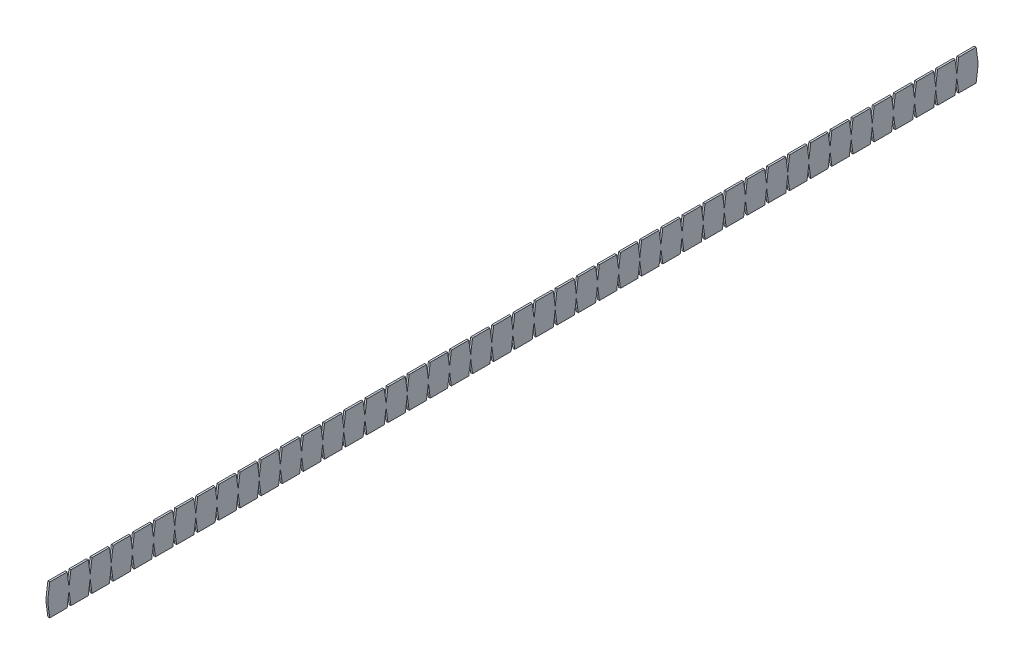
SolidWorks part; units mm, degrees
ref_plane "Front Plane" through (0, 0, 0) normal (0, 0, 1) x (1, 0, 0)
ref_plane "Top Plane" through (0, 0, 0) normal (0, 1, 0) x (1, 0, 0)
ref_plane "Right Plane" through (0, 0, 0) normal (1, 0, 0) x (0, 0, -1)
sketch "Sketch2" plane through (0, 0, 0) normal (1, 0, 0) x (0, 0, -1)
  line L9 (-34.544, 0) -> (-31.496, 22.86)
  line L10 (-31.496, 22.86) -> (-3.048, 22.86)
  line L94 (-3.048, 22.86) -> (0, 0)
  line L187 (-34.544, 0) -> (-34.544, -5.08)
  line L255 (-3.048, -27.94) -> (0, -5.08)
  line L256 (-31.496, -27.94) -> (-3.048, -27.94)
  line L257 (-34.544, -5.08) -> (-31.496, -27.94)
  line L262 (0, 0) -> (0, -5.08)
  dimension "D1" = 28.448
  dimension "D2" = 34.544
  dimension "D3" = 5.08
  dimension "D4" = 50.8
extrude "Boss-Extrude1" add sketch "Sketch2" along normal blind 3.048
pattern_linear "LPattern1" count 44 spacing 34.544 along (0, 0, -1) of "Boss-Extrude1"
